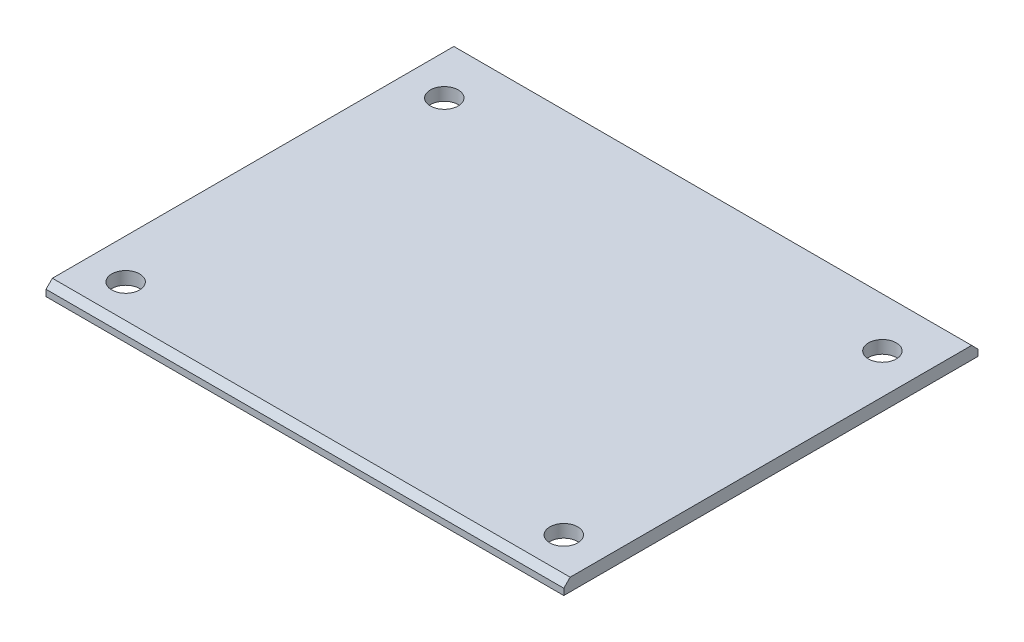
SolidWorks part; units mm, degrees
ref_plane "Front Plane" through (0, 0, 0) normal (0, 0, 1) x (1, 0, 0)
ref_plane "Top Plane" through (0, 0, 0) normal (0, 1, 0) x (1, 0, 0)
ref_plane "Right Plane" through (0, 0, 0) normal (1, 0, 0) x (0, 0, -1)
sketch "Sketch1" plane through (0, 0, 0) normal (0, 1, 0) x (1, 0, 0)
  line L1 (-32.5, 26) -> (32.5, 26)
  line L2 (-32.5, 26) -> (-32.5, -26)
  line L3 (-32.5, -26) -> (32.5, -26)
  line L4 (32.5, 26) -> (32.5, -26)
  line L5 (-32.5, 26) -> (32.5, -26) construction
  line L6 (-32.5, -26) -> (32.5, 26) construction
  point P0 (0, 0)
  dimension "D1" = 65
  dimension "D2" = 52
extrude "Boss-Extrude1" add sketch "Sketch1" along normal blind 1.6
sketch "Sketch2" plane through (0, 1.6, 0) normal (0, 1, 0) x (1, 0, 0)
  line L0 (-32.5, -26) -> (32.5, -26) construction
  line L1 (-32.5, 26) -> (-32.5, -26) construction
  line L2 (32.5, 26) -> (-32.5, 26) construction
  line L3 (32.5, -26) -> (32.5, 26) construction
  circle A0 centre (-27.5, -21) radius 1.75
  circle A1 centre (-27.5, 19) radius 1.75
  circle A2 centre (27.5, 19) radius 1.75
  circle A3 centre (27.5, -21) radius 1.75
  dimension "D1" = 3.5
  dimension "D2" = 5
  dimension "D3" = 5
  dimension "D4" = 7
  dimension "D5" = 5
extrude "Cut-Extrude1" cut sketch "Sketch2" against normal through all
chamfer "Chamfer1" distance 0.8 distance2 0.8 2 edges at (0, 1.6, -26) (0, 1.6, 26)
